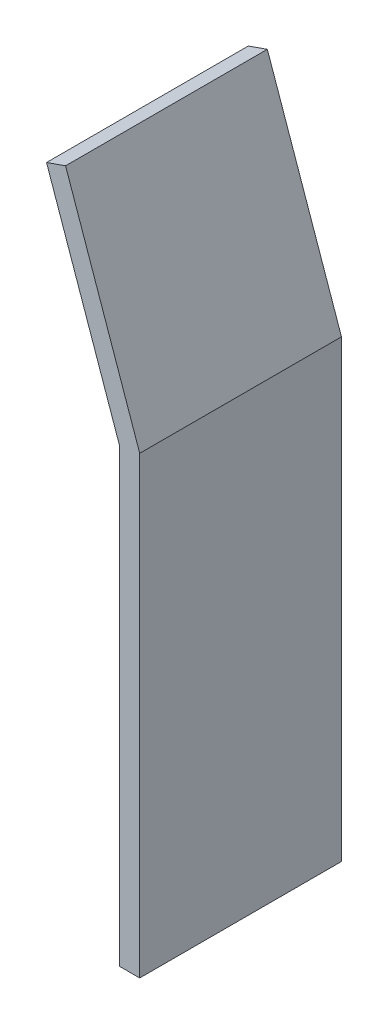
SolidWorks part; units mm, degrees
ref_plane "Front" through (0, 0, 0) normal (0, 0, 1) x (1, 0, 0)
ref_plane "Top" through (0, 0, 0) normal (0, 1, 0) x (1, 0, 0)
ref_plane "Right" through (0, 0, 0) normal (1, 0, 0) x (0, 0, -1)
sketch "Sketch1" plane through (0, 0, 0) normal (0, 0, 1) x (1, 0, 0)
  line L0 (0, 0) -> (0, -447)
  line L1 (0, -447) -> (20, -447)
  line L2 (20, -447) -> (20, 3.3971)
  line L4 (-53.485, 213.4724) -> (-72.3633, 206.8687)
  line L5 (-72.3633, 206.8687) -> (0, 0)
  line L6 (-53.485, 213.4724) -> (20, 3.3971)
  dimension "D1" = 20
  dimension "D2" = 20
  dimension "D3" = 447
  dimension "D4" = 219.16
  dimension "D5" = 160.72
  dimension "D6" = 222.5571
extrude "Boss-Extrude1" add sketch "Sketch1" along normal blind 200
